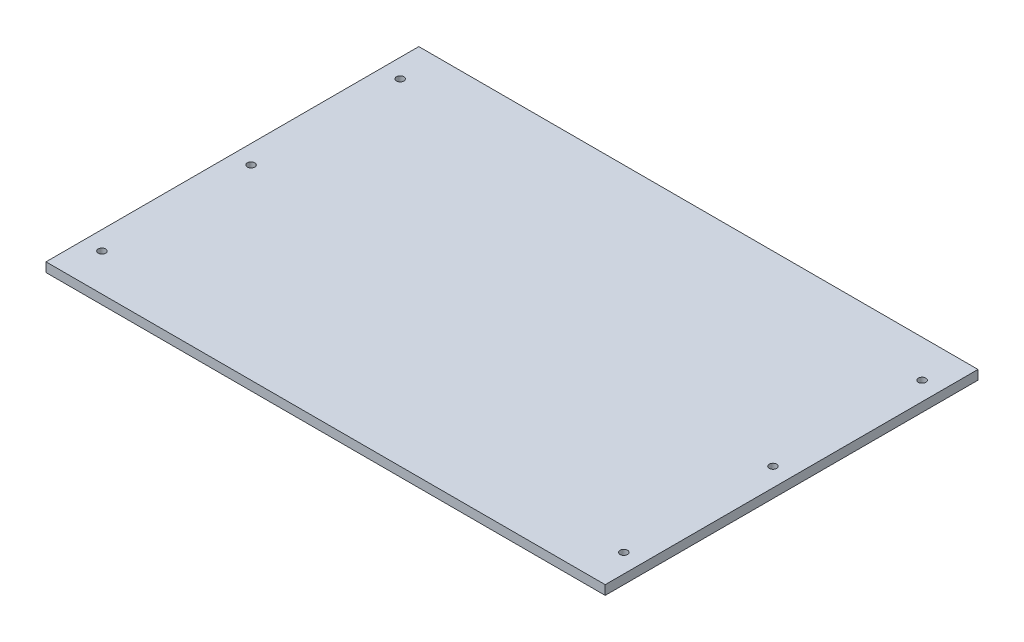
SolidWorks part; units mm, degrees
ref_plane "Front Plane" through (0, 0, 0) normal (0, 0, 1) x (1, 0, 0)
ref_plane "Top Plane" through (0, 0, 0) normal (0, 1, 0) x (1, 0, 0)
ref_plane "Right Plane" through (0, 0, 0) normal (1, 0, 0) x (0, 0, -1)
sketch "Sketch1" plane through (0, 0, 0) normal (0, 1, 0) x (1, 0, 0)
  line L0 (-140, 100) -> (-140, -100) construction
  line L1 (-150, -100) -> (150, -100)
  line L2 (-150, -100) -> (-150, 100)
  line L3 (-150, 100) -> (150, 100)
  line L4 (150, -100) -> (150, 100)
  line L5 (-150, -100) -> (150, 100) construction
  line L6 (-150, 100) -> (150, -100) construction
  line L7 (-2.75, 0) -> (2.75, 0) construction
  line L8 (0, -2.75) -> (0, 2.75) construction
  circle A0 centre (-140, 80) radius 2
  circle A1 centre (-140, -80) radius 2
  circle A2 centre (-140, 0) radius 2
  circle A3 centre (140, -80) radius 2
  circle A4 centre (140, 0) radius 2
  circle A5 centre (140, 80) radius 2
  point P0 (0, 0)
  dimension "D5" = 4
  dimension "D1" = 200
  dimension "D2" = 300
  dimension "D3" = 10
  dimension "D4" = 20
extrude "Boss-Extrude1" add sketch "Sketch1" along normal blind 5
